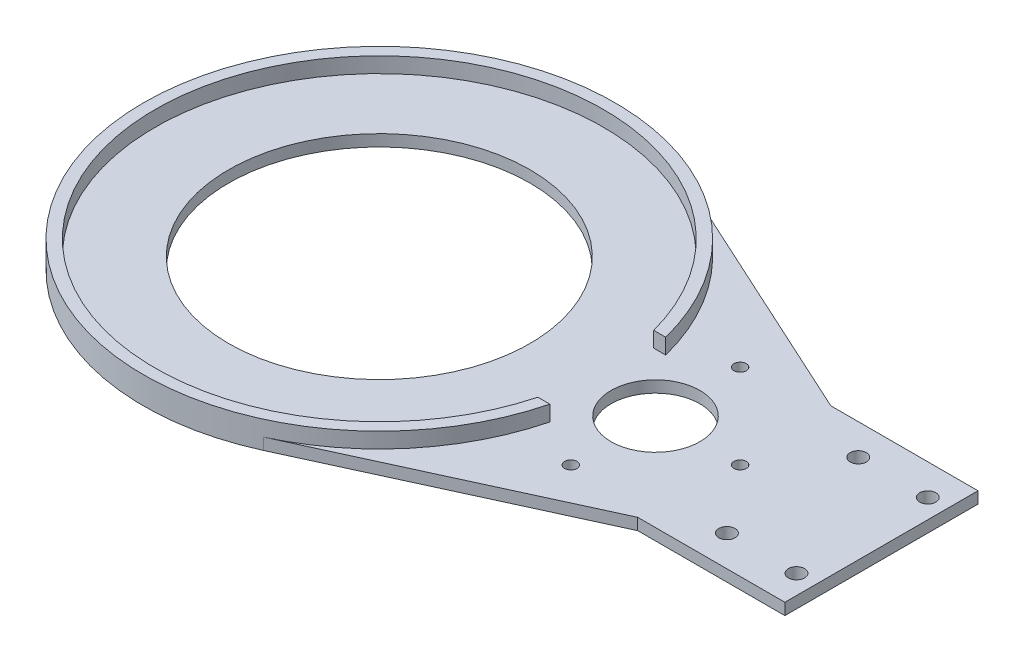
SolidWorks part; units mm, degrees
ref_plane "前视基准面" through (0, 0, 0) normal (0, 0, 1) x (1, 0, 0)
ref_plane "上视基准面" through (0, 0, 0) normal (0, 1, 0) x (1, 0, 0)
ref_plane "右视基准面" through (0, 0, 0) normal (1, 0, 0) x (0, 0, -1)
sketch "草图2" plane through (0, 0, 0) normal (0, 1, 0) x (1, 0, 0)
  line L0 (91.9019, 25) -> (25.4317, 55.4732)
  line L1 (91.9019, 25) -> (130, 25)
  line L3 (91.9019, -25) -> (130, -25)
  line L4 (130, 25) -> (130, -25)
  line L5 (91.9019, -25) -> (25.4317, -55.4732)
  line L6 (0, 0) -> (130, 0) construction
  line L7 (91.9019, 25) -> (91.9019, -25) construction
  arc A0 (25.4317, 55.4732) -> (25.4317, -55.4732) centre (0, 0) ccw
  dimension "D1" = 122.05
  dimension "D3" = 38.0981
  dimension "D4" = 130
  dimension "D2" = 50
extrude "凸台-拉伸3" add sketch "草图2" along normal blind 3
sketch "草图3" plane through (0, 3, 0) normal (0, 1, 0) x (1, 0, 0)
  line L0 (-70.5368, 0) -> (164.9091, 0) construction
  line L5 (130, -25) -> (130, 25) construction
  line L6 (130, 25) -> (91.9019, 25) construction
  line L7 (71.5, 55.0155) -> (71.5, -34.2154) construction
  line L9 (0, 51.0329) -> (0, -40.488) construction
  circle A4 centre (71.5, 0) radius 11.5
  circle A5 centre (0, 0) radius 39
  circle A8 centre (71.5, 21.917) radius 1.6
  circle A9 centre (93.417, 0) radius 1.6
  circle A11 centre (71.5, -21.917) radius 1.6
  circle A12 centre (125, 17) radius 2.1
  circle A13 centre (107, 17) radius 2.1
  circle A14 centre (125, -17) radius 2.1
  circle A15 centre (107, -17) radius 2.1
  point P0 (0, 0)
  dimension "D3" = 3.2
  dimension "D4" = 43.834
  dimension "D8" = 23
  dimension "D9" = 78
  dimension "D2" = 3.2
  dimension "D10" = 4.2
  dimension "D11" = 4.2
  dimension "D1" = 71.5
  dimension "D5" = 21.917
  dimension "D6" = 5
  dimension "D7" = 8
  dimension "D12" = 8
  dimension "D13" = 18
extrude "切除-拉伸1" cut sketch "草图3" against normal through all
sketch "草图4" plane through (0, 0, 0) normal (0, 0, 1) x (1, 0, 0)
  line L0 (0, 38.1765) -> (0, -19.0651) construction
  line L1 (-61.025, 3) -> (-58.025, 3)
  line L2 (-61.025, 3) -> (-61.025, 7)
  line L3 (-61.025, 7) -> (-58.025, 7)
  line L4 (-58.025, 3) -> (-58.025, 7)
  dimension "D1" = 4
  dimension "D2" = 3
revolve "旋转1" add sketch "草图4" angle 360 about L0
ref_plane "基准面1" through (61.025, 0, 0) normal (1, 0, 0) x (0, 0, -1)
sketch "草图6" plane through (61.025, 0, 0) normal (1, 0, 0) x (0, 0, -1)
  line L0 (0, 0) -> (0, 9.4535) construction
  line L1 (-25, 3) -> (25, 3) construction
  line L2 (15, 3) -> (-15, 3)
  line L4 (15, 13) -> (-15, 13)
  line L5 (-15, 3) -> (-15, 13)
  line L6 (15, 3) -> (15, 13)
  point P10 (0, 3)
  point P11 (0, 13)
  dimension "D1" = 30
  dimension "D2" = 10
extrude "切除-拉伸3" cut sketch "草图6" against normal blind 10
